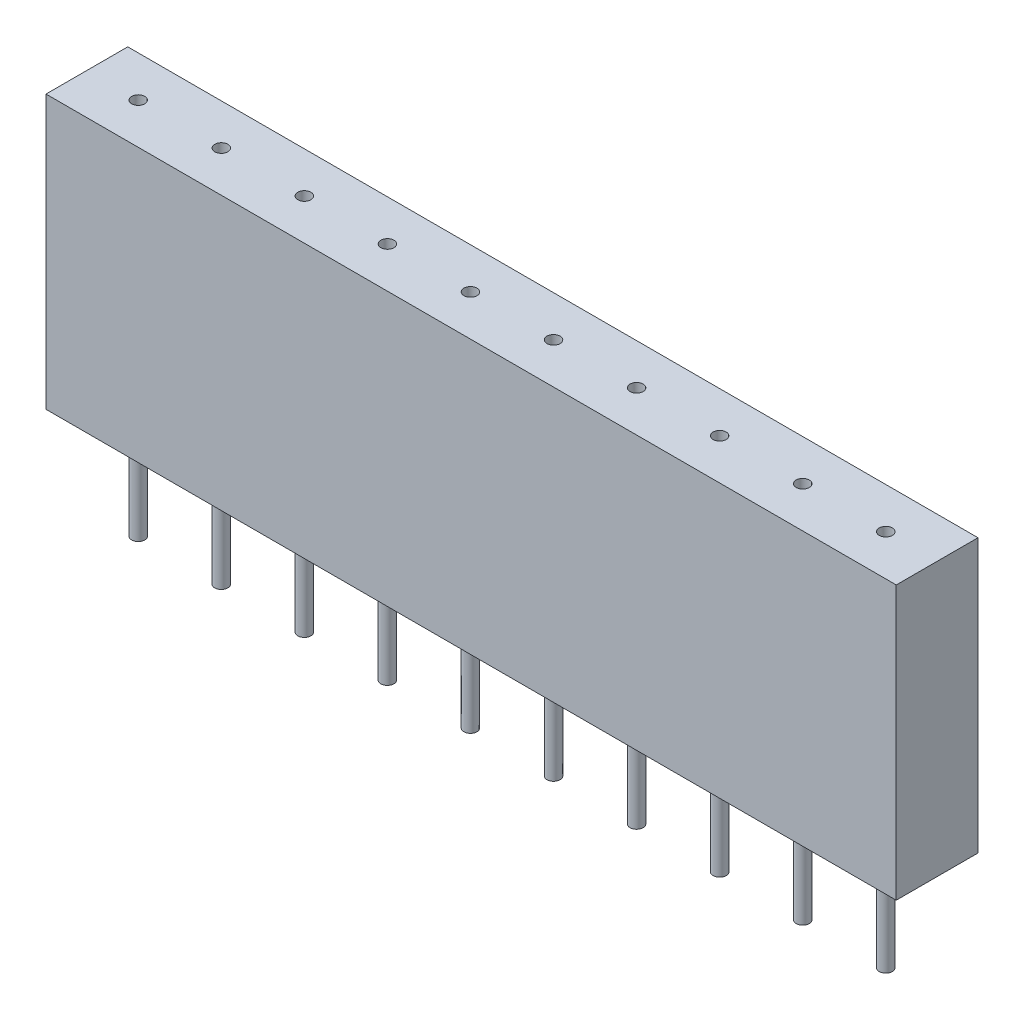
SolidWorks part; units mm, degrees
ref_plane "Front Plane" through (0, 0, 0) normal (0, 0, 1) x (1, 0, 0)
ref_plane "Top Plane" through (0, 0, 0) normal (0, 1, 0) x (1, 0, 0)
ref_plane "Right Plane" through (0, 0, 0) normal (1, 0, 0) x (0, 0, -1)
sketch "Sketch1" plane through (0, 0, 0) normal (0, 1, 0) x (1, 0, 0)
  line L1 (-13, -1.25) -> (13, -1.25)
  line L2 (-13, -1.25) -> (-13, 1.25)
  line L3 (-13, 1.25) -> (13, 1.25)
  line L4 (13, -1.25) -> (13, 1.25)
  line L5 (-13, -1.25) -> (13, 1.25) construction
  line L6 (-13, 1.25) -> (13, -1.25) construction
  point P0 (0, 0)
  dimension "D1" = 26
  dimension "D2" = 2.5
extrude "Boss-Extrude1" add sketch "Sketch1" along normal blind 8.35
sketch "Sketch2" plane through (0, 8.35, 0) normal (0, 1, 0) x (1, 0, 0)
  line L0 (-13, 0) -> (13, 0) construction
  line L1 (-13, 1.25) -> (-13, -1.25) construction
  line L2 (13, -1.25) -> (13, 1.25) construction
  circle A0 centre (-11.43, 0) radius 0.2
  dimension "D1" = 0.4
  dimension "D2" = 1.57
extrude "Cut-Extrude1" cut sketch "Sketch2" against normal blind 3
sketch "Sketch3" plane through (0, 0, 0) normal (0, -1, 0) x (1, 0, 0)
  line L0 (-13, -1.25) -> (-13, 1.25) construction
  circle A0 centre (-11.43, 0) radius 0.2
  dimension "D1" = 0.4
  dimension "D2" = 1.57
extrude "Boss-Extrude2" add sketch "Sketch3" along normal blind 3.2
pattern_linear "LPattern1" count 10 spacing 2.54 along (1, 0, 0) of "Cut-Extrude1", "Boss-Extrude2"
